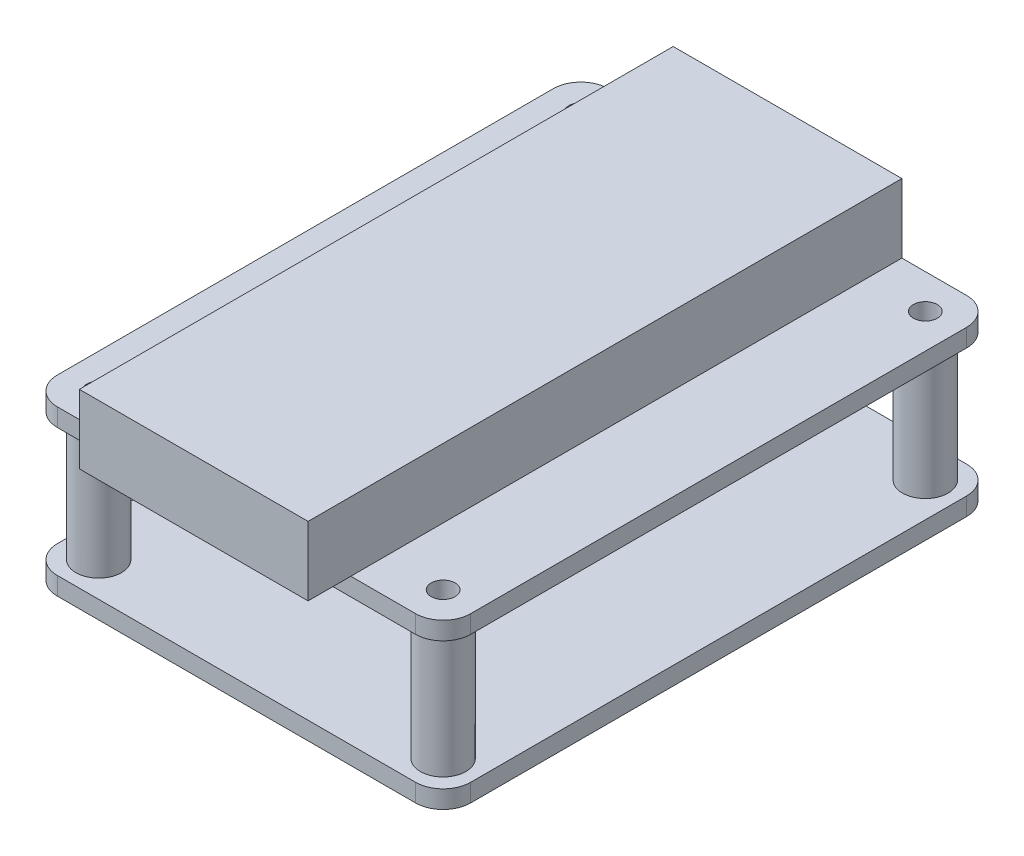
SolidWorks part; units mm, degrees
ref_plane "Front Plane" through (0, 0, 0) normal (0, 0, 1) x (1, 0, 0)
ref_plane "Top Plane" through (0, 0, 0) normal (0, 1, 0) x (1, 0, 0)
ref_plane "Right Plane" through (0, 0, 0) normal (1, 0, 0) x (0, 0, -1)
sketch "Sketch1" plane through (0, 0, 0) normal (0, 1, 0) x (1, 0, 0)
  line L0 (0, 22.225) -> (-3.175, 22.225) construction
  line L1 (0, 0) -> (31.75, 0) construction
  line L2 (0, 0) -> (0, 44.45) construction
  line L3 (0, 44.45) -> (31.75, 44.45) construction
  line L4 (31.75, 0) -> (31.75, 44.45) construction
  line L5 (-0.635, -3.175) -> (32.385, -3.175)
  line L6 (-3.175, -0.635) -> (-3.175, 45.085)
  line L7 (-0.635, 47.625) -> (32.385, 47.625)
  line L8 (34.925, -0.635) -> (34.925, 45.085)
  line L9 (15.875, 44.45) -> (15.875, 47.625) construction
  arc A0 (-0.635, -3.175) -> (-3.175, -0.635) centre (-0.635, -0.635) cw
  arc A1 (32.385, -3.175) -> (34.925, -0.635) centre (32.385, -0.635) ccw
  arc A2 (32.385, 47.625) -> (34.925, 45.085) centre (32.385, 45.085) cw
  arc A3 (-3.175, 45.085) -> (-0.635, 47.625) centre (-0.635, 45.085) cw
  circle A4 centre (0, 44.45) radius 1.1
  circle A5 centre (31.75, 44.45) radius 1.1
  circle A6 centre (31.75, 0) radius 1.1
  circle A7 centre (0, 0) radius 1.1
  point P12 (-3.175, -3.175)
  point P17 (34.925, 47.625)
  point P20 (-3.175, 47.625)
  dimension "D5" = 2.54
  dimension "D6" = 2.2
  dimension "D1" = 31.75
  dimension "D2" = 44.45
  dimension "D3" = 50.8
  dimension "D4" = 38.1
extrude "Boss-Extrude1" add sketch "Sketch1" along normal blind 1.651
ref_plane "Plane1" through (0, 15.113, 0) normal (0, -1, 0) x (-1, 0, 0)
sketch "Sketch2" plane through (0, 15.113, 0) normal (0, -1, 0) x (-1, 0, 0)
  line L4 (3.175, -0.635) -> (3.175, 45.085)
  line L5 (0.635, 47.625) -> (-32.385, 47.625)
  line L6 (-34.925, 45.085) -> (-34.925, -0.635)
  line L7 (-32.385, -3.175) -> (0.635, -3.175)
  line L8 (3.175, -0.635) -> (3.175, 45.085)
  line L9 (0.635, 47.625) -> (-32.385, 47.625)
  line L10 (-34.925, 45.085) -> (-34.925, -0.635)
  line L11 (-32.385, -3.175) -> (0.635, -3.175)
  circle A1 centre (-31.75, 44.45) radius 1.1
  circle A2 centre (-31.75, 44.45) radius 1.1
  circle A3 centre (0, 44.45) radius 1.1
  arc A4 (0.635, -3.175) -> (3.175, -0.635) centre (0.635, -0.635) ccw
  arc A5 (3.175, 45.085) -> (0.635, 47.625) centre (0.635, 45.085) ccw
  arc A6 (-32.385, 47.625) -> (-34.925, 45.085) centre (-32.385, 45.085) ccw
  arc A7 (-34.925, -0.635) -> (-32.385, -3.175) centre (-32.385, -0.635) ccw
  arc A8 (0.635, -3.175) -> (3.175, -0.635) centre (0.635, -0.635) ccw
  arc A9 (3.175, 45.085) -> (0.635, 47.625) centre (0.635, 45.085) ccw
  arc A10 (-32.385, 47.625) -> (-34.925, 45.085) centre (-32.385, 45.085) ccw
  arc A11 (-34.925, -0.635) -> (-32.385, -3.175) centre (-32.385, -0.635) ccw
  circle A12 centre (0, 44.45) radius 1.1
  circle A13 centre (-31.75, 0) radius 1.1
  circle A14 centre (-31.75, 0) radius 1.1
  circle A15 centre (0, 0) radius 1.1
  circle A16 centre (0, 0) radius 1.1
  dimension "D1" = 0
  dimension "D2" = 0
  dimension "D3" = 0
  dimension "D4" = 0
  dimension "D5" = 0
extrude "Boss-Extrude2" add sketch "Sketch2" along normal blind 1.651 separate body
sketch "Sketch3" plane through (0, 1.651, 0) normal (0, 1, 0) x (1, 0, 0)
  circle A0 centre (0, 0) radius 2.1
  circle A1 centre (31.75, 44.45) radius 1.1
  circle A2 centre (31.75, 44.45) radius 1.1
  circle A3 centre (0, 44.45) radius 1.1
  circle A4 centre (0, 44.45) radius 1.1
  circle A5 centre (31.75, 0) radius 1.1
  circle A6 centre (31.75, 0) radius 1.1
  circle A7 centre (0, 0) radius 1.1
  circle A8 centre (0, 0) radius 1.1
  circle A9 centre (31.75, 0) radius 2.1
  circle A10 centre (31.75, 44.45) radius 2.1
  circle A11 centre (0, 44.45) radius 2.1
  dimension "D1" = 0
  dimension "D2" = 0
  dimension "D3" = 0
  dimension "D4" = 0
  dimension "D5" = 1
extrude "Boss-Extrude3" add sketch "Sketch3" along normal up to surface (11.811 mm away) up to face at (31.75, 13.462, -1.1)
sketch "Sketch4" plane through (0, 15.113, 0) normal (0, 1, 0) x (1, 0, 0)
  line L0 (-0.635, 47.625) -> (32.385, 47.625) construction
  line L1 (5.334, 47.625) -> (26.416, 47.625)
  line L2 (5.334, 47.625) -> (5.334, -7.112)
  line L3 (5.334, -7.112) -> (26.416, -7.112)
  line L4 (26.416, 47.625) -> (26.416, -7.112)
  line L5 (32.385, -3.175) -> (-0.635, -3.175) construction
  point P4 (15.875, 47.625)
  point P5 (15.875, 47.625)
  point P6 (15.875, 47.625)
  dimension "D1" = 21.082
  dimension "D2" = 3.937
extrude "Boss-Extrude4" add sketch "Sketch4" along normal blind 6.35
